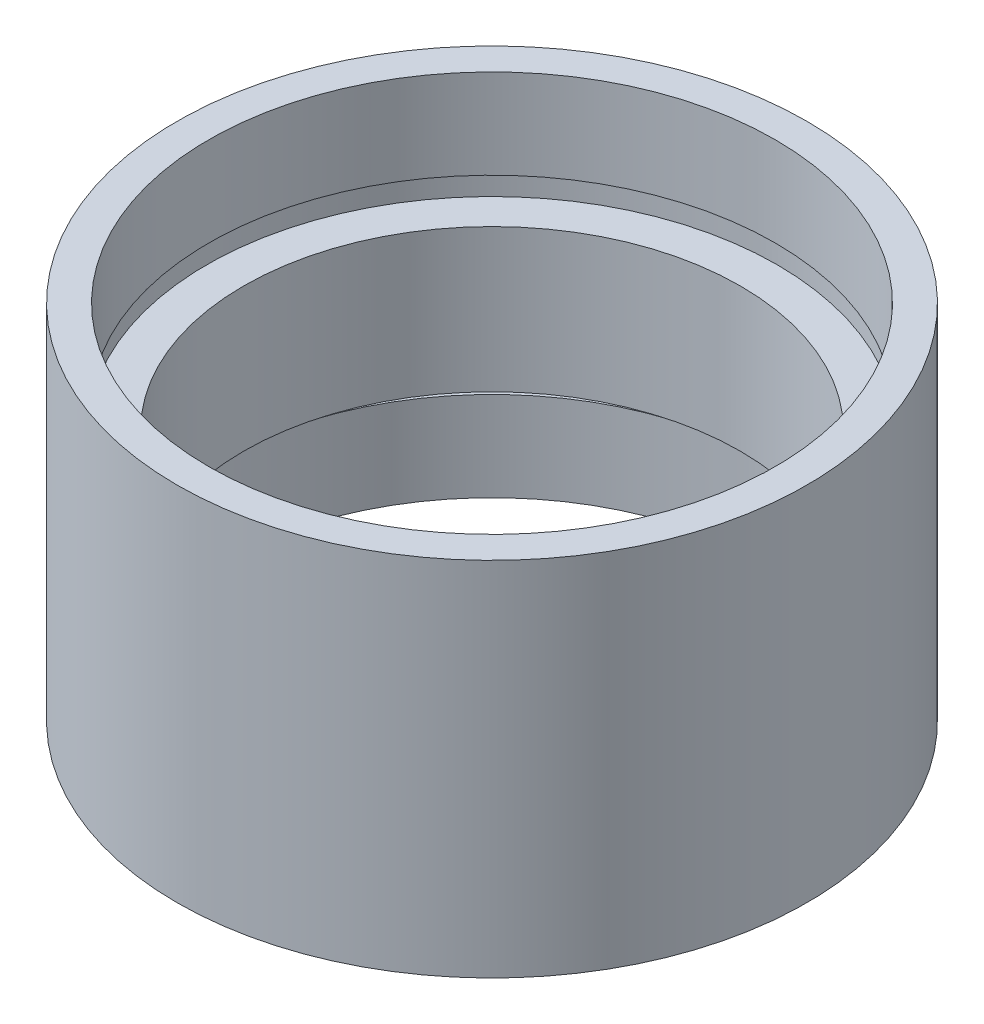
SolidWorks part; units mm, degrees
ref_plane "前视基准面" through (0, 0, 0) normal (0, 0, 1) x (1, 0, 0)
ref_plane "上视基准面" through (0, 0, 0) normal (0, 1, 0) x (1, 0, 0)
ref_plane "右视基准面" through (0, 0, 0) normal (1, 0, 0) x (0, 0, -1)
sketch "草图1" plane through (0, 0, 0) normal (0, 0, 1) x (1, 0, 0)
  line L0 (0, 161.3762) -> (0, 0) construction
  line L1 (141.7365, 0) -> (-131.7984, 0) construction
  line L2 (13.75, 0) -> (13.75, 4.5)
  line L3 (15.85, 0) -> (15.85, 18.2)
  line L4 (14.35, 4.5) -> (14.35, 5.5)
  line L5 (13.75, 4.5) -> (14.35, 4.5)
  line L6 (12.5, 5.5) -> (12.5, 12.7)
  line L7 (12.5, 5.5) -> (14.35, 5.5)
  line L8 (14.25, 18.2) -> (14.25, 13.7)
  line L9 (15.85, 18.2) -> (14.25, 18.2)
  line L10 (14.35, 13.7) -> (14.35, 12.7)
  line L11 (14.25, 13.7) -> (14.35, 13.7)
  line L12 (12.5, 12.7) -> (14.35, 12.7)
  line L13 (13.75, 0) -> (15.85, 0)
  dimension "D1" = 13.75
  dimension "D2" = 15.85
  dimension "D3" = 14.35
  dimension "D4" = 12.5
  dimension "D5" = 4.5
  dimension "D6" = 1
  dimension "D7" = 12.7
  dimension "D8" = 14.25
  dimension "D9" = 14.35
  dimension "D10" = 1
  dimension "D11" = 4.5
revolve "旋转1" add sketch "草图1" angle 360 about L0
cosmetic thread "装饰螺纹线1"
cosmetic thread "装饰螺纹线2"
cosmetic thread "装饰螺纹线3"
